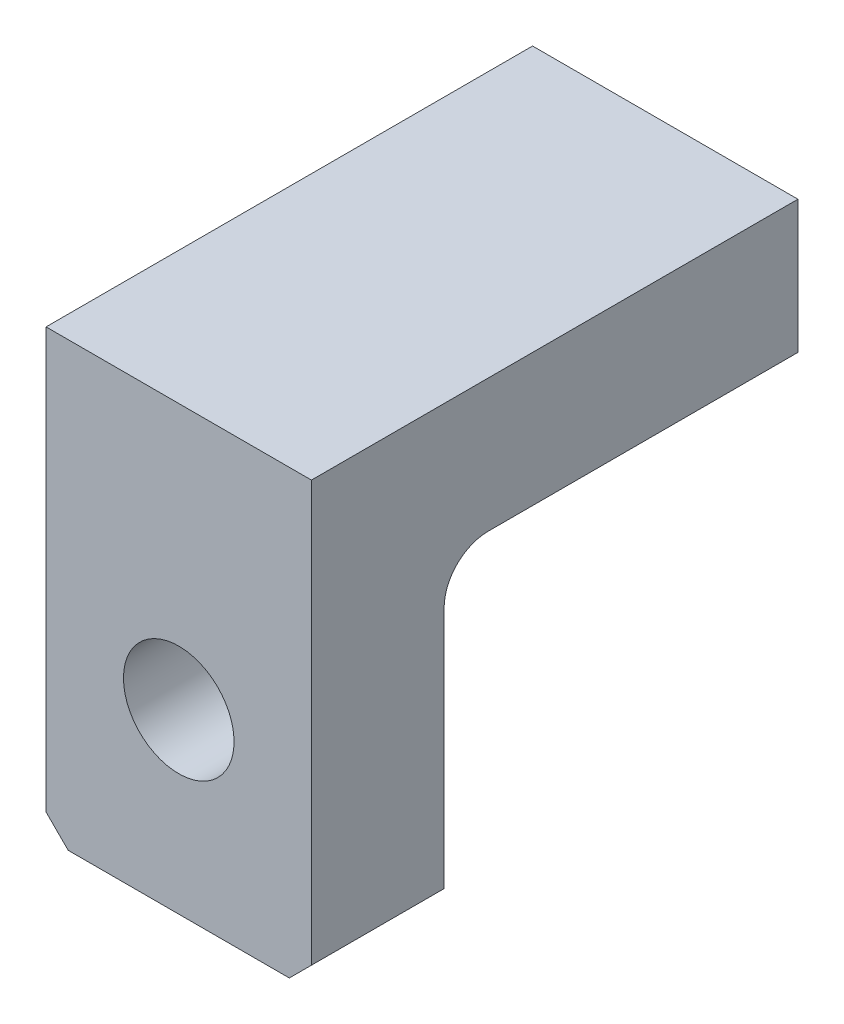
SolidWorks part; units mm, degrees
ref_plane "Přední rovina" through (0, 0, 0) normal (0, 0, 1) x (1, 0, 0)
ref_plane "Vrchní rovina" through (0, 0, 0) normal (0, 1, 0) x (1, 0, 0)
ref_plane "Pravá rovina" through (0, 0, 0) normal (1, 0, 0) x (0, 0, -1)
sketch "Skica1" plane through (0, 0, 0) normal (0, 0, 1) x (1, 0, 0)
  line L1 (0, 0) -> (60, 0)
  line L2 (0, 0) -> (0, 100)
  line L3 (0, 100) -> (60, 100)
  line L4 (60, 0) -> (60, 100)
  dimension "D1" = 100
  dimension "D2" = 60
extrude "Přidat vysunutím1" add sketch "Skica1" along normal blind 30
sketch "Skica2" plane through (0, 0, 0) normal (0, 0, -1) x (-1, 0, 0)
  line L0 (0, 100) -> (0, 0) construction
  line L1 (-60, 100) -> (0, 100)
  line L2 (-60, 100) -> (-60, 70)
  line L3 (-60, 70) -> (0, 70)
  line L4 (0, 100) -> (0, 70)
  dimension "D1" = 30
extrude "Přidat vysunutím2" add sketch "Skica2" along normal blind 80
sketch "Skica3" plane through (0, 0, 0) normal (0, 0, -1) x (-1, 0, 0)
  line L0 (-60, 0) -> (-60, 70) construction
  line L1 (0, 0) -> (-60, 0) construction
  circle A0 centre (-30, 40) radius 12.5
  point P4 (-30, 36.2789)
  dimension "D2" = 25
  dimension "D3" = 40
  dimension "D1" = 30
extrude "Odebrat vysunutím1" cut sketch "Skica3" against normal blind 80
fillet "Zaoblit2" radius 10 1 edges at (30, 70, 0)
chamfer "Zkosení1" distance 5 angle 45 2 edges at (0, 0, 15) (60, 0, 15)
